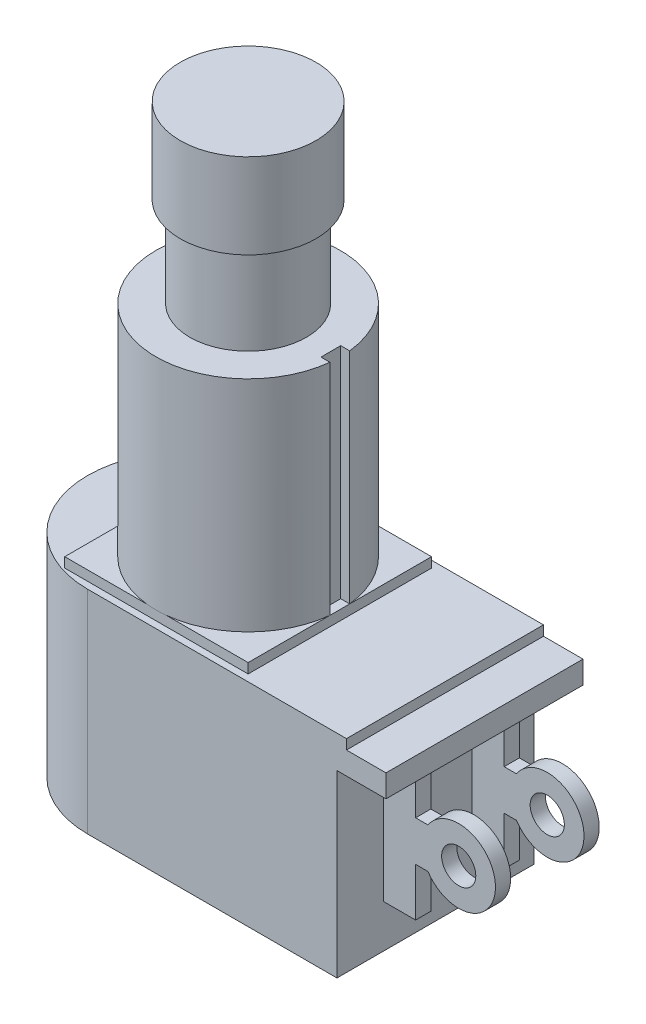
SolidWorks part; units mm, degrees
ref_plane "Front Plane" through (0, 0, 0) normal (0, 0, 1) x (1, 0, 0)
ref_plane "Top Plane" through (0, 0, 0) normal (0, 1, 0) x (1, 0, 0)
ref_plane "Right Plane" through (0, 0, 0) normal (1, 0, 0) x (0, 0, -1)
sketch "Sketch1" plane through (0, 0, 0) normal (0, 0, 1) x (1, 0, 0)
  line L0 (0, 31.196) -> (0, -7.3236) construction
  line L1 (0, 0) -> (5.925, 0)
  line L2 (5.925, 0) -> (5.925, 14.0843)
  line L3 (5.925, 14.0843) -> (3.75, 14.0843)
  line L4 (3.75, 14.0843) -> (3.75, 19.8755)
  line L5 (3.75, 19.8755) -> (4.3625, 19.8755)
  line L6 (4.3625, 19.8755) -> (4.3625, 25.3365)
  line L7 (4.3625, 25.3365) -> (0, 25.3365)
  line L8 (0, 25.3365) -> (0, 0)
  point P11 (0, 15.0992)
  point P12 (0, 25.2901)
  point P13 (0, 31.196)
  dimension "D1" = 11.85
  dimension "D2" = 7.5
  dimension "D3" = 8.7249
  dimension "D4" = 14.0843
  dimension "D5" = 5.7912
  dimension "D6" = 5.461
revolve "Revolve1" add sketch "Sketch1" angle 360 about L0
sketch "Sketch2" plane through (0, 0, 0) normal (0, -1, 0) x (1, 0, 0)
  line L1 (-5.8928, -5.8928) -> (5.8928, -5.8928)
  line L2 (-5.8928, -5.8928) -> (-5.8928, 5.8928)
  line L3 (-5.8928, 5.8928) -> (5.8928, 5.8928)
  line L4 (5.8928, -5.8928) -> (5.8928, 5.8928)
  line L5 (-5.8928, -5.8928) -> (5.8928, 5.8928) construction
  line L6 (-5.8928, 5.8928) -> (5.8928, -5.8928) construction
  point P0 (0, 0)
  dimension "D1" = 11.7856
extrude "Boss-Extrude1" add sketch "Sketch2" along normal blind 0.635
sketch "Sketch3" plane through (0, -0.635, 0) normal (0, -1, 0) x (1, 0, 0)
  line L1 (-3.9815, 6.331) -> (12.6492, 6.331)
  line L3 (-3.9814, -6.331) -> (12.6492, -6.331)
  line L4 (12.6492, 6.331) -> (12.6492, -6.331)
  arc A0 (-3.9814, -6.331) -> (-3.9815, 6.331) centre (-3.9814, 0) cw
  point P4 (12.6492, 0)
  point P7 (-10.3124, 0)
  dimension "D2" = 22.9616
  dimension "D1" = 12.6619
  dimension "D3" = 12.6492
extrude "Boss-Extrude2" add sketch "Sketch3" along normal blind 0.635
sketch "Sketch4" plane through (0, -1.27, 0) normal (0, -1, 0) x (1, 0, 0)
  line L0 (-3.9814, -6.331) -> (12.6492, -6.331) construction
  line L1 (12.6492, 6.331) -> (-3.9815, 6.331) construction
  line L2 (-3.9814, -6.331) -> (15.1892, -6.3309)
  line L3 (15.1892, 6.3309) -> (-3.9815, 6.331)
  line L4 (15.1892, 6.3309) -> (15.1892, -6.3309)
  arc A0 (-3.9815, 6.331) -> (-3.9814, -6.331) centre (-3.9814, 0) ccw construction
  arc A1 (-3.9815, 6.331) -> (-3.9814, -6.331) centre (-3.9814, 0) ccw
  point P5 (14.651, -6.2558)
  point P7 (-10.3124, 0)
  dimension "D1" = 25.5016
extrude "Boss-Extrude3" add sketch "Sketch4" along normal blind 1.4478
sketch "Sketch5" plane through (0, -2.7178, 0) normal (0, -1, 0) x (1, 0, 0)
  line L0 (15.1892, 6.3309) -> (-3.9815, 6.331) construction
  line L1 (-3.9814, -6.331) -> (15.1892, -6.3309) construction
  line L2 (12.0396, 6.3309) -> (-3.9815, 6.331)
  line L3 (-3.9814, -6.331) -> (12.0396, -6.3309)
  line L4 (12.0396, -6.3309) -> (12.0396, 6.3309)
  arc A0 (-3.9815, 6.331) -> (-3.9814, -6.331) centre (-3.9814, 0) ccw construction
  arc A1 (-3.9815, 6.331) -> (-3.9814, -6.331) centre (-3.9814, 0) ccw
  point P3 (16.4332, 6.3309)
  point P7 (-10.3124, 0)
  dimension "D1" = 22.352
extrude "Boss-Extrude4" add sketch "Sketch5" along normal blind 11.5443
ref_plane "Plane1" through (0, 0, 3.3338) normal (0, 0, 1) x (1, 0, 0)
sketch "Sketch6" plane through (0, 0, 3.3338) normal (0, 0, 1) x (1, 0, 0)
  line L0 (14.097, -8.4074) -> (14.097, -11.5062)
  line L1 (12.0396, -2.7178) -> (14.097, -2.7178)
  line L2 (12.0396, -2.7178) -> (12.0396, -11.5062)
  line L3 (12.0396, -11.5062) -> (14.097, -11.5062)
  line L4 (14.097, -2.7178) -> (14.097, -5.8166)
  line L5 (14.097, -5.8166) -> (14.8903, -5.8166)
  line L6 (12.0396, -7.112) -> (21.43, -7.112) construction
  line L7 (14.097, -8.4074) -> (14.8903, -8.4074)
  arc A0 (14.8903, -8.4074) -> (14.8903, -5.8166) centre (16.8656, -7.112) ccw
  circle A1 centre (16.8656, -7.112) radius 1.0985
  point P15 (19.2278, -7.112)
  dimension "D3" = 2.5908
  dimension "D4" = 4.7244
  dimension "D6" = 2.1971
  dimension "D1" = 8.7884
  dimension "D2" = 2.0574
  dimension "D5" = 5.1308
extrude "Boss-Extrude5" add sketch "Sketch6" against normal blind 0.9779
mirror "Mirror1" about plane through (0, 0, 0) normal (0, 0, 1) of "Boss-Extrude5"
sketch "Sketch7" plane through (0, 14.0843, 0) normal (0, 1, 0) x (1, 0, 0)
  line L1 (5.3155, 0.635) -> (6.8253, 0.635)
  line L2 (5.3155, 0.635) -> (5.3155, -0.635)
  line L3 (5.3155, -0.635) -> (6.8253, -0.635)
  line L4 (6.8253, 0.635) -> (6.8253, -0.635)
  point P4 (5.3155, 0)
  dimension "D1" = 1.27
extrude "Cut-Extrude1" cut sketch "Sketch7" against normal up to surface (14.0843 mm away) up to face at (4.4457, 0, 4.4457)
